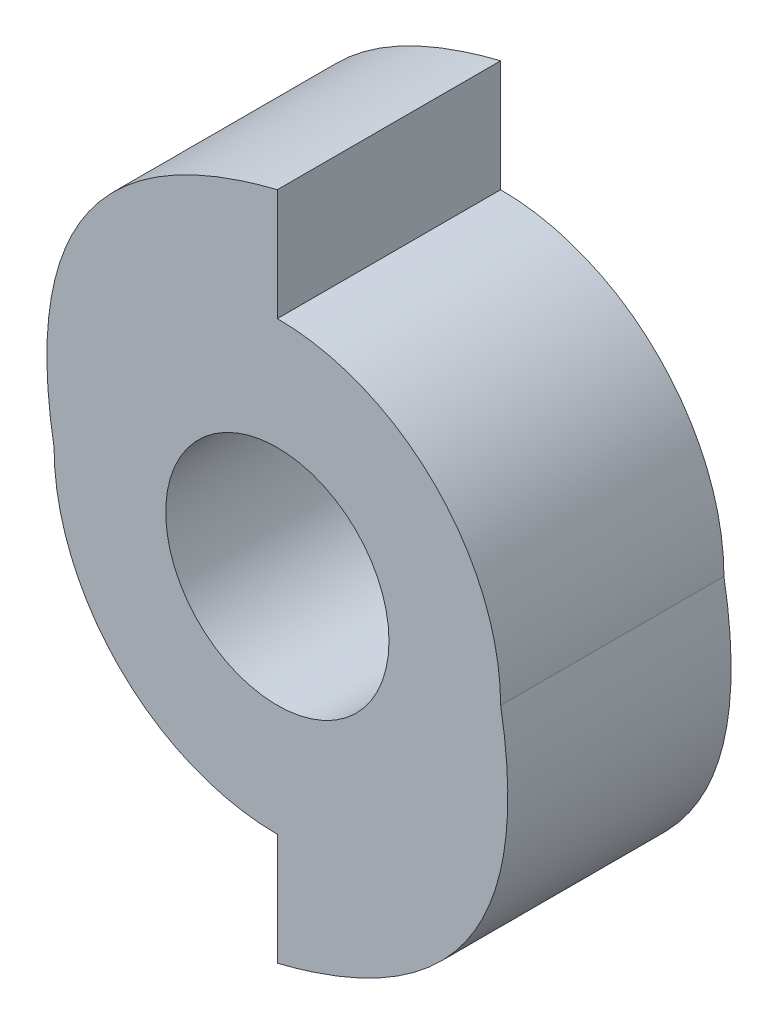
SolidWorks part; units mm, degrees
material "ABS"
ref_plane "Front Plane" through (0, 0, 0) normal (0, 0, 1) x (1, 0, 0)
ref_plane "Top Plane" through (0, 0, 0) normal (0, 1, 0) x (1, 0, 0)
ref_plane "Right Plane" through (0, 0, 0) normal (1, 0, 0) x (0, 0, -1)
sketch "Sketch1" plane through (0, 0, 0) normal (0, 0, 1) x (1, 0, 0)
  circle B0 centre (95.0986, 21.4684) radius 3.175
  line B1 (95.0986, 30.9934) -> (95.0986, 27.8184)
  arc B2 (101.4486, 21.4684) -> (95.0986, 27.8184) centre (95.0986, 21.4684) ccw
  spline B3 degree 2 poles (101.4486, 21.4684) (102.8072, 13.8548) (95.0986, 11.9434) knots 0 0 0 1 1 1
  line B4 (95.0986, 11.9434) -> (95.0986, 15.1184)
  arc B5 (88.7486, 21.4684) -> (95.0986, 15.1184) centre (95.0986, 21.4684) ccw
  spline B6 degree 2 poles (88.7486, 21.4684) (87.39, 29.082) (95.0986, 30.9934) knots 0 0 0 1 1 1
  circle B7 centre (108.2067, 20.3632) radius 3.175
  line B8 (108.2067, 10.8382) -> (108.2067, 14.0132)
  spline B9 degree 2 poles (114.5567, 20.3632) (115.9153, 12.7495) (108.2067, 10.8382) knots 0 0 0 1 1 1
  arc B10 (114.5567, 20.3632) -> (108.2067, 26.7132) centre (108.2067, 20.3632) ccw
  line B11 (108.2067, 29.8882) -> (108.2067, 26.7132)
  spline B12 degree 2 poles (101.8567, 20.3632) (100.4982, 27.9768) (108.2067, 29.8882) knots 0 0 0 1 1 1
  arc B13 (101.8567, 20.3632) -> (108.2067, 14.0132) centre (108.2067, 20.3632) ccw
sketch_block_instance "CLUTCH_CUTFILE-1"
sketch_block "CLUTCH_CUTFILE"
sketch "Sketch2" plane through (0, 0, 0) normal (0, 0, 1) x (1, 0, 0)
  line L0 (95.0986, 30.9934) -> (95.0986, 27.8184) construction
  line L1 (95.0986, 11.9434) -> (95.0986, 15.1184) construction
  line L2 (108.2067, 10.8382) -> (108.2067, 14.0132) construction
  line L3 (108.2067, 29.8882) -> (108.2067, 26.7132) construction
  line L4 (95.0986, 30.9934) -> (95.0986, 27.8184)
  line L5 (95.0986, 11.9434) -> (95.0986, 15.1184)
  line L6 (108.2067, 10.8382) -> (108.2067, 14.0132)
  line L7 (108.2067, 29.8882) -> (108.2067, 26.7132)
  circle A0 centre (95.0986, 21.4684) radius 3.175 construction
  arc A1 (101.4486, 21.4684) -> (95.0986, 27.8184) centre (95.0986, 21.4684) ccw construction
  arc A2 (88.7486, 21.4684) -> (95.0986, 15.1184) centre (95.0986, 21.4684) ccw construction
  circle A3 centre (108.2067, 20.3632) radius 3.175 construction
  arc A4 (114.5567, 20.3632) -> (108.2067, 26.7132) centre (108.2067, 20.3632) ccw construction
  arc A5 (101.8567, 20.3632) -> (108.2067, 14.0132) centre (108.2067, 20.3632) ccw construction
  circle A6 centre (95.0986, 21.4684) radius 3.175
  arc A7 (101.4486, 21.4684) -> (95.0986, 27.8184) centre (95.0986, 21.4684) ccw
  arc A8 (88.7486, 21.4684) -> (95.0986, 15.1184) centre (95.0986, 21.4684) ccw
  circle A9 centre (108.2067, 20.3632) radius 3.175
  arc A10 (114.5567, 20.3632) -> (108.2067, 26.7132) centre (108.2067, 20.3632) ccw
  arc A11 (101.8567, 20.3632) -> (108.2067, 14.0132) centre (108.2067, 20.3632) ccw
  parabola Q0 (101.4486, 21.4684) -> (95.0986, 11.9434) focus (98.0415, 17.0441) apex (100.6289, 15.4169) construction
  parabola Q1 (88.7486, 21.4684) -> (95.0986, 30.9934) focus (92.1557, 25.8927) apex (89.5684, 27.5198) construction
  parabola Q2 (114.5567, 20.3632) -> (108.2067, 10.8382) focus (111.1496, 15.9389) apex (113.737, 14.3117) construction
  parabola Q3 (101.8567, 20.3632) -> (108.2067, 29.8882) focus (105.2639, 24.7874) apex (102.6765, 26.4146) construction
  parabola Q4 (101.4486, 21.4684) -> (95.0986, 11.9434) focus (98.0415, 17.0441) apex (100.6289, 15.4169)
  parabola Q5 (88.7486, 21.4684) -> (95.0986, 30.9934) focus (92.1557, 25.8927) apex (89.5684, 27.5198)
  parabola Q6 (114.5567, 20.3632) -> (108.2067, 10.8382) focus (111.1496, 15.9389) apex (113.737, 14.3117)
  parabola Q7 (101.8567, 20.3632) -> (108.2067, 29.8882) focus (105.2639, 24.7874) apex (102.6765, 26.4146)
extrude "Boss-Extrude1" add sketch "Sketch2" along normal blind 6.35 contours Q5 A8 L5 Q4 A7 L4 A6
